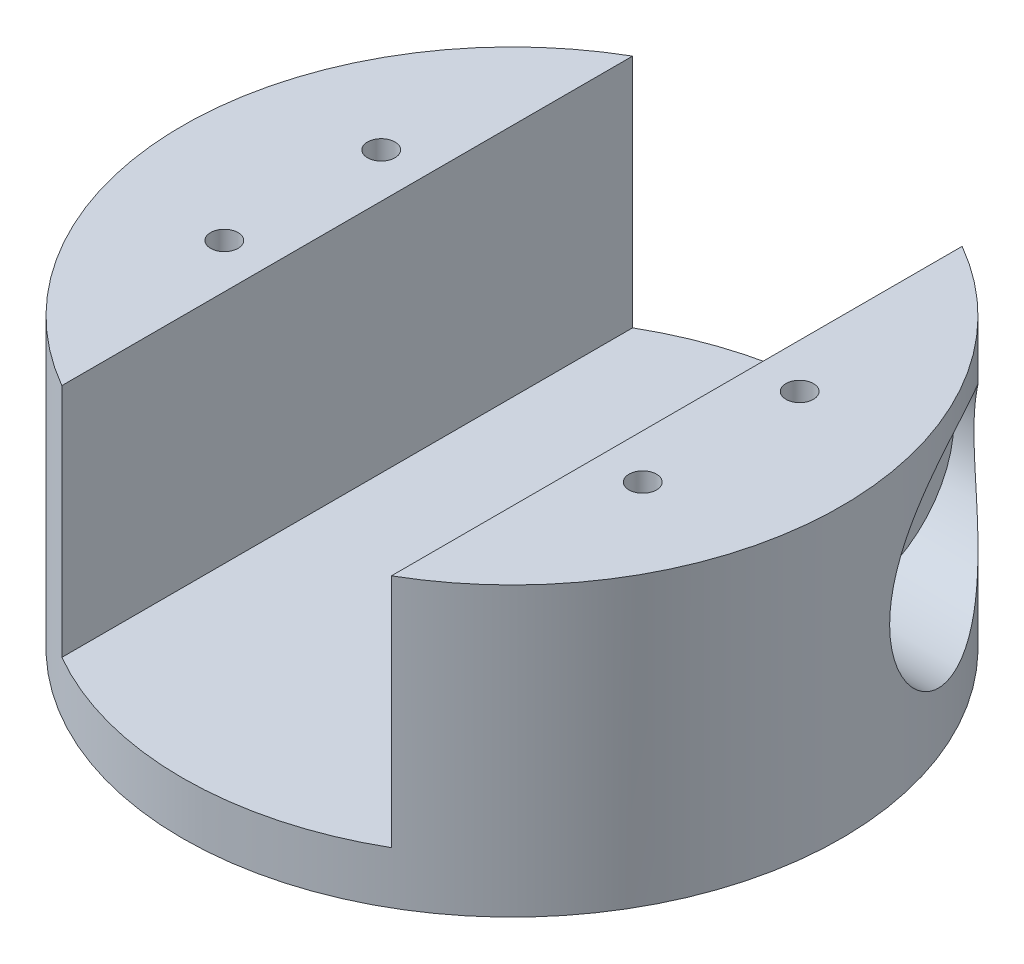
SolidWorks part; units mm, degrees
ref_plane "Front Plane" through (0, 0, 0) normal (0, 0, 1) x (1, 0, 0)
ref_plane "Top Plane" through (0, 0, 0) normal (0, 1, 0) x (1, 0, 0)
ref_plane "Right Plane" through (0, 0, 0) normal (1, 0, 0) x (0, 0, -1)
sketch "Sketch1" plane through (0, 0, 0) normal (0, 1, 0) x (1, 0, 0)
  circle A0 centre (0, 0) radius 17.5
  dimension "D1" = 35
extrude "Boss-Extrude1" add sketch "Sketch1" along normal blind 15
sketch "Sketch2" plane through (0, 15, 0) normal (0, 1, 0) x (1, 0, 0)
  circle A0 centre (0, 0) radius 63
  dimension "D1" = 126
extrude "Boss-Extrude2" add sketch "Sketch2" along normal blind 10
sketch "Sketch4" plane through (0, 25, 0) normal (0, 1, 0) x (1, 0, 0)
  line L0 (-31.5, 44) -> (-31.5, 54.5596)
  line L2 (-31.5, -44) -> (-31.5, 44)
  line L4 (31.5, -44) -> (31.5, 44)
  line L5 (-31.5, -44) -> (31.5, 44) construction
  line L6 (-31.5, 44) -> (31.5, -44) construction
  line L7 (31.5, 44) -> (31.5, 54.5596)
  line L8 (31.5, -44) -> (31.5, -54.5596)
  line L9 (-31.5, -44) -> (-31.5, -54.5596)
  circle A0 centre (0, 0) radius 63 construction
  arc A3 (-31.5, -54.5596) -> (-31.5, 54.5596) centre (0, 0) cw
  arc A4 (31.5, 54.5596) -> (31.5, -54.5596) centre (0, 0) cw
  point P0 (0, 0)
  dimension "D1" = 88
  dimension "D2" = 63
extrude "Boss-Extrude3" add sketch "Sketch4" along normal blind 45
sketch "Sketch5" plane through (0, 70, 0) normal (0, 1, 0) x (1, 0, 0)
  line L0 (-40, 48.6724) -> (-40, -48.6724) construction
  line L1 (0, -13.75) -> (0, 13.75) construction
  line L2 (-13.75, 0) -> (13.75, 0) construction
  line L3 (40, 48.6724) -> (40, -48.6724) construction
  arc A0 (-31.5, 54.5596) -> (-31.5, -54.5596) centre (0, 0) ccw construction
  circle A1 centre (-40, 15) radius 2.625
  circle A2 centre (-40, -15) radius 2.625
  circle A3 centre (40, -15) radius 2.625
  circle A4 centre (40, 15) radius 2.625
  dimension "D4" = 5.25
  dimension "D1" = 40
  dimension "D2" = 30
  dimension "D3" = 15
extrude "Cut-Extrude1" cut sketch "Sketch5" against normal blind 6
ref_plane "Plane1" through (63, 0, 0) normal (1, 0, 0) x (0, 0, -1)
sketch "Sketch7" plane through (63, 0, 0) normal (1, 0, 0) x (0, 0, -1)
  line L0 (0, 38.5) -> (0, -38.5) construction
  line L1 (54.5596, 70) -> (-54.5596, 70) construction
  circle A0 centre (30, 45) radius 20
  dimension "D1" = 40
  dimension "D2" = 30
  dimension "D3" = 25
extrude "Cut-Extrude2" cut sketch "Sketch7" against normal offset from surface (28.5 mm away) 3 up to face at (31.5, 47.5, 0)
sketch "Sketch9" plane through (63, 0, 0) normal (1, 0, 0) x (0, 0, -1)
  line L0 (30, 45) -> (21.0197, 36.0197) construction
  line L1 (30, 45) -> (17.3, 45) construction
  circle A0 centre (30, 45) radius 12.7 construction
  circle A1 centre (21.0197, 36.0197) radius 2
  circle A5 centre (21.0197, 53.9803) radius 2
  circle A6 centre (38.9803, 53.9803) radius 2
  circle A7 centre (38.9803, 36.0197) radius 2
  circle A8 centre (30, 45) radius 6.5
  point P15 (22.5, 57.5)
  point P16 (30, 45)
  dimension "D1" = 25.4
  dimension "D2" = 4
  dimension "D5" = 13
  dimension "D3" = 45
  dimension "D4" = 4
extrude "Cut-Extrude3" cut sketch "Sketch9" against normal up to surface (31.5 mm away) up to face at (31.5, 47.5, 0)
